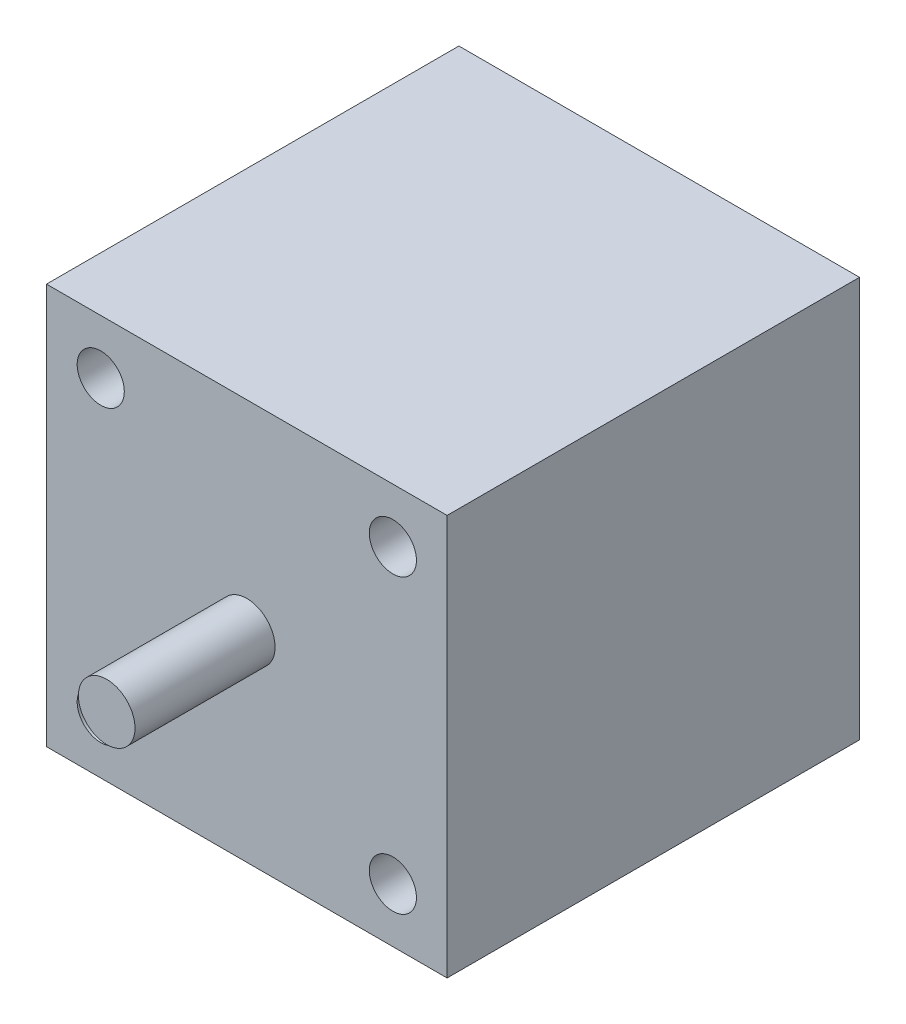
SolidWorks part; units mm, degrees
ref_plane "Front Plane" through (0, 0, 0) normal (0, 0, 1) x (1, 0, 0)
ref_plane "Top Plane" through (0, 0, 0) normal (0, 1, 0) x (1, 0, 0)
ref_plane "Right Plane" through (0, 0, 0) normal (1, 0, 0) x (0, 0, -1)
sketch "Sketch1" plane through (0, 0, 0) normal (0, 0, 1) x (1, 0, 0)
  line L1 (-21.25, -21.25) -> (21.25, -21.25)
  line L2 (-21.25, -21.25) -> (-21.25, 21.25)
  line L3 (-21.25, 21.25) -> (21.25, 21.25)
  line L4 (21.25, -21.25) -> (21.25, 21.25)
  line L5 (-21.25, -21.25) -> (21.25, 21.25) construction
  line L6 (-21.25, 21.25) -> (21.25, -21.25) construction
  point P0 (0, 0)
  dimension "D1" = 42.5
  dimension "D2" = 42.5
extrude "Boss-Extrude1" add sketch "Sketch1" along normal blind 43.75
sketch "Sketch2" plane through (0, 0, 43.75) normal (0, 0, 1) x (1, 0, 0)
  line L0 (21.25, -21.25) -> (21.25, 21.25) construction
  line L1 (21.25, 21.25) -> (-21.25, 21.25) construction
  circle A0 centre (-15.495, 15.495) radius 2.5
  circle A1 centre (15.495, 15.495) radius 2.5
  circle A2 centre (15.495, -15.495) radius 2.5
  circle A3 centre (-15.495, -15.495) radius 2.5
  point P0 (0, 0)
  dimension "D3" = 30.99
  dimension "D1" = 30.99
  dimension "D2" = 30.99
  dimension "D4" = 5.755
  dimension "D5" = 5.755
  dimension "D6" = 30.99
  dimension "D7" = 5.755
extrude "Cut-Extrude1" cut sketch "Sketch2" against normal blind 5
sketch "Sketch3" plane through (0, 0, 43.75) normal (0, 0, 1) x (1, 0, 0)
  circle A0 centre (0, 0) radius 3
extrude "Boss-Extrude2" add sketch "Sketch3" along normal blind 14.86
